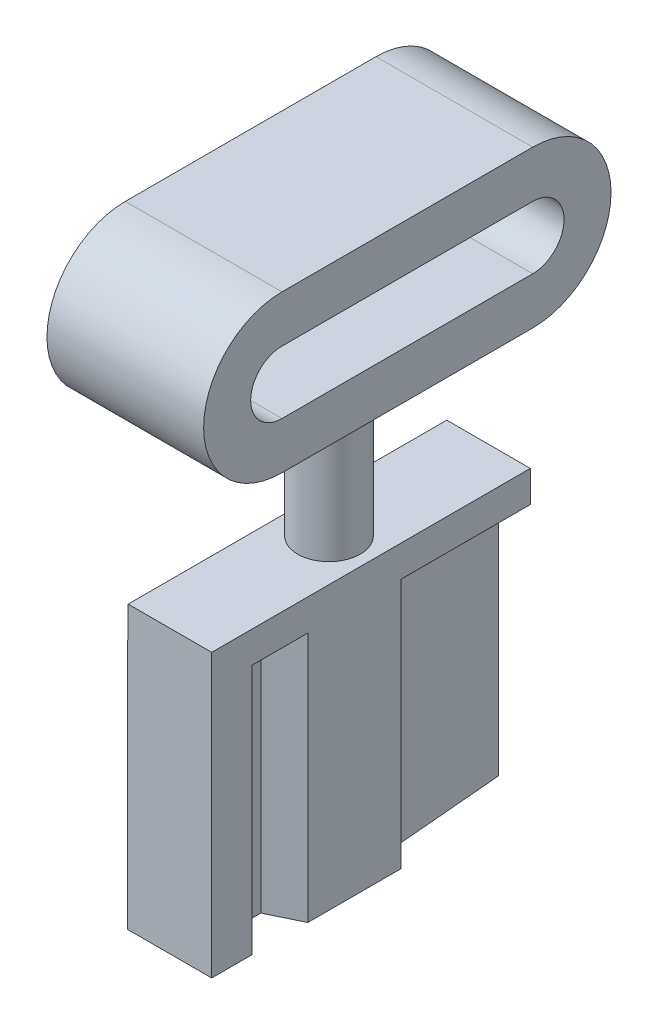
SolidWorks part; units mm, degrees
ref_plane "Front Plane" through (0, 0, 0) normal (0, 0, 1) x (1, 0, 0)
ref_plane "Top Plane" through (0, 0, 0) normal (0, 1, 0) x (1, 0, 0)
ref_plane "Right Plane" through (0, 0, 0) normal (1, 0, 0) x (0, 0, -1)
sketch "Sketch7" plane through (0, 0, 0) normal (0, 1, 0) x (1, 0, 0)
  line L0 (-1.3406, -5.0835) -> (-1.3406, -1.4962)
  line L1 (-1.3406, -1.4962) -> (-0.2532, -1.2643)
  line L2 (-0.2532, -1.2643) -> (-0.2532, -0.2185)
  line L3 (-0.2532, -0.2185) -> (-1.1287, 0.6571)
  line L4 (-1.1287, 0.6571) -> (-0.9585, 5.0835)
  line L5 (-0.9585, 5.0835) -> (0.3305, 5.0835)
  line L6 (0.3305, 5.0835) -> (0.6345, 1.5448)
  line L7 (0.6345, 1.5448) -> (1.3406, 0.9505)
  line L8 (1.3406, 0.9505) -> (1.3406, -2.0182)
  line L9 (1.3406, -2.0182) -> (0.3305, -2.5047)
  line L10 (0.3305, -2.5047) -> (0.3305, -3.2899)
  line L11 (0.3305, -3.2899) -> (1.3406, -3.7937)
  line L12 (1.3406, -3.7937) -> (1.3406, -5.0835)
  line L13 (1.3406, -5.0835) -> (-1.3406, -5.0835)
extrude "Boss-Extrude1" add sketch "Sketch7" against normal blind 8
sketch "Sketch8" plane through (0, 0, 0) normal (0, 1, 0) x (1, 0, 0)
  line L0 (0.3305, 5.0835) -> (-0.9585, 5.0835) construction
  line L1 (1.3406, -5.0835) -> (-1.3255, -5.0835)
  line L2 (1.3406, -5.0835) -> (1.3406, 5.0835)
  line L3 (1.3406, 5.0835) -> (-1.3255, 5.0835)
  line L4 (-1.3255, -5.0835) -> (-1.3255, 5.0835)
extrude "Boss-Extrude2" add sketch "Sketch8" along normal blind 1
sketch "Sketch9" plane through (0, 1, 0) normal (0, 1, 0) x (1, 0, 0)
  circle A0 centre (0, 0) radius 1
  dimension "D1" = 2
extrude "Boss-Extrude3" add sketch "Sketch9" along normal blind 5
sketch "Sketch11" plane through (0, 0, 0) normal (1, 0, 0) x (0, 0, -1)
  line L5 (-4, 8.5) -> (4, 8.5) construction
  line L6 (-4, 11) -> (4, 11)
  line L7 (-4, 6) -> (4, 6)
  line L8 (1, 6) -> (-1, 6) construction
  line L9 (-4, 8.5) -> (4, 8.5) construction
  line L10 (-4, 9.5) -> (4, 9.5)
  line L11 (-4, 7.5) -> (4, 7.5)
  arc A4 (-4, 11) -> (-4, 6) centre (-4, 8.5) ccw
  arc A5 (4, 6) -> (4, 11) centre (4, 8.5) ccw
  arc A6 (-4, 9.5) -> (-4, 7.5) centre (-4, 8.5) ccw
  arc A7 (4, 7.5) -> (4, 9.5) centre (4, 8.5) ccw
  point P2 (0, 8.5)
  point P11 (0, 8.5)
  dimension "D1" = 2.5
  dimension "D3" = 1
  dimension "D2" = 8
extrude "Boss-Extrude4" add sketch "Sketch11" along normal mid plane 5
